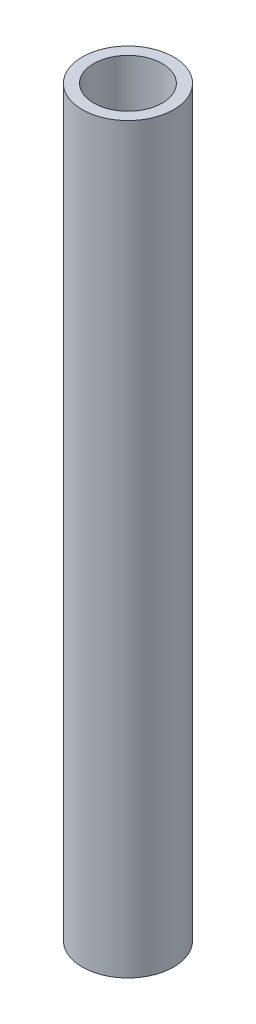
SolidWorks part; units mm, degrees
ref_plane "Front" through (0, 0, 0) normal (0, 0, 1) x (1, 0, 0)
ref_plane "Top" through (0, 0, 0) normal (0, 1, 0) x (1, 0, 0)
ref_plane "Right" through (0, 0, 0) normal (1, 0, 0) x (0, 0, -1)
sketch "草图1" plane through (0, 0, 0) normal (0, 1, 0) x (1, 0, 0)
  circle A0 centre (0, 0) radius 8
  circle A1 centre (0, 0) radius 6
extrude "凸台-拉伸1" add sketch "草图1" along normal blind 130
